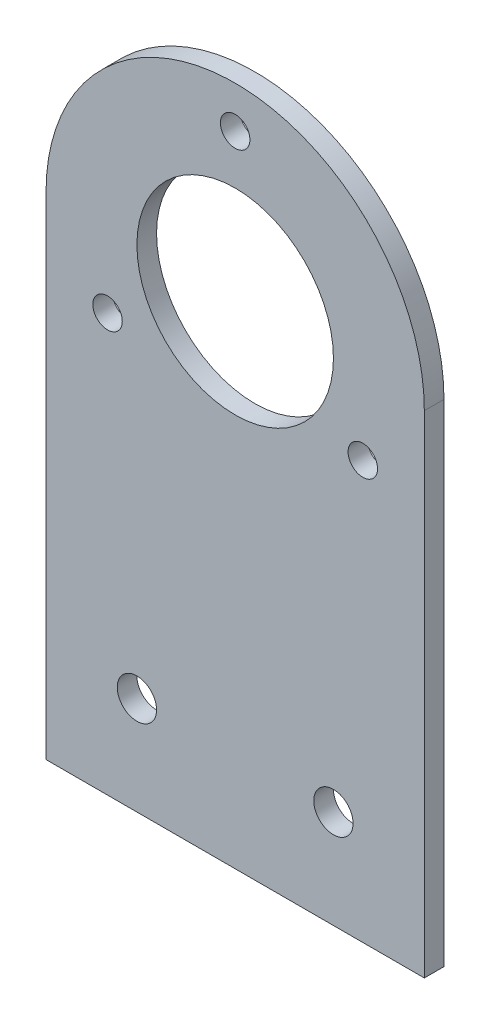
SolidWorks part; units mm, degrees
ref_plane "Ön Düzlem" through (0, 0, 0) normal (0, 0, 1) x (1, 0, 0)
ref_plane "Üst Düzlem" through (0, 0, 0) normal (0, 1, 0) x (1, 0, 0)
ref_plane "Sağ Düzlem" through (0, 0, 0) normal (1, 0, 0) x (0, 0, -1)
sketch "Sketch1" plane through (0, 0, 0) normal (0, 0, 1) x (1, 0, 0)
  line L1 (-19.25, 25) -> (19.25, 25) construction
  line L2 (-19.25, 25) -> (-19.25, -25)
  line L3 (-19.25, -25) -> (19.25, -25)
  line L4 (19.25, 25) -> (19.25, -25)
  line L5 (-19.25, 25) -> (19.25, -25) construction
  line L6 (-19.25, -25) -> (19.25, 25) construction
  arc A0 (-19.25, 25) -> (19.25, 25) centre (0, 25) cw
  circle A1 centre (0, 25) radius 10
  circle A2 centre (0, 40) radius 1.5
  circle A3 centre (-10, -15) radius 2
  circle A4 centre (10, -15) radius 2
  circle A5 centre (12.9904, 17.5) radius 1.5
  circle A6 centre (0, 25) radius 10
  circle A7 centre (-12.9904, 17.5) radius 1.5
  circle A8 centre (0, 25) radius 10
  point P0 (0, 0)
  point P23 (0, 25)
  dimension "D3" = 20
  dimension "D4" = 3
  dimension "D6" = 4
  dimension "D1" = 38.5
  dimension "D2" = 50
  dimension "D5" = 15
  dimension "D7" = 10
  dimension "D8" = 20
  dimension "D9" = 9.25
  dimension "D10" = 3
extrude "Boss-Extrude1" add sketch "Sketch1" along normal blind 2 contours A0 L2 L3 L4 A7 A5 A4 A3 A2 A1
